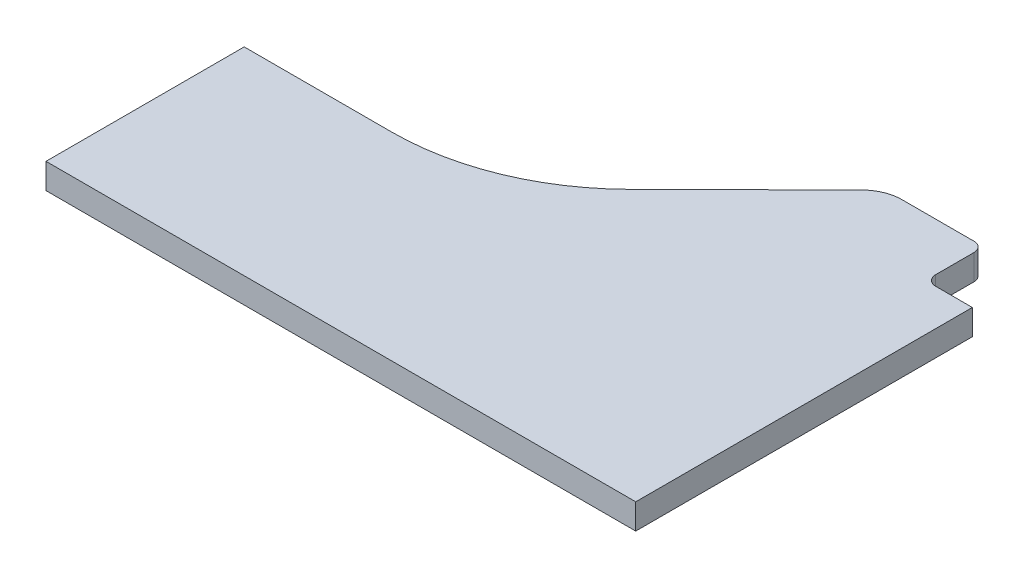
SolidWorks part; units mm, degrees
ref_plane "Front Plane" through (0, 0, 0) normal (0, 0, 1) x (1, 0, 0)
ref_plane "Top Plane" through (0, 0, 0) normal (0, 1, 0) x (1, 0, 0)
ref_plane "Right Plane" through (0, 0, 0) normal (1, 0, 0) x (0, 0, -1)
sketch "Sketch1" plane through (0, 0, 0) normal (0, 1, 0) x (1, 0, 0)
  line L0 (0, 0) -> (295, 0)
  line L1 (0, 0) -> (0, 99.1471)
  line L2 (265.9473, 197.4908) -> (230.6444, 197.4908)
  line L3 (295, 0) -> (295, 168.379)
  line L4 (295, 168.379) -> (276.6155, 168.379)
  line L5 (271.6155, 173.379) -> (271.6155, 192.5357)
  line L7 (158.1533, 133.8685) -> (216.5735, 191.7039)
  line L8 (0, 99.1471) -> (73.7284, 99.1471)
  arc A0 (271.6155, 192.5357) -> (265.9473, 197.4908) centre (266.6155, 192.5357) ccw
  arc A1 (271.6155, 173.379) -> (276.6155, 168.379) centre (276.6155, 173.379) ccw
  arc A2 (216.5735, 191.7039) -> (230.6444, 197.4908) centre (230.6444, 177.4908) cw
  arc A3 (73.7284, 99.1471) -> (158.1533, 133.8685) centre (73.7284, 219.1471) ccw
  dimension "D1" = 5
  dimension "D2" = 20
  dimension "D3" = 120
extrude "Boss-Extrude1" add sketch "Sketch1" along normal blind 12.7
